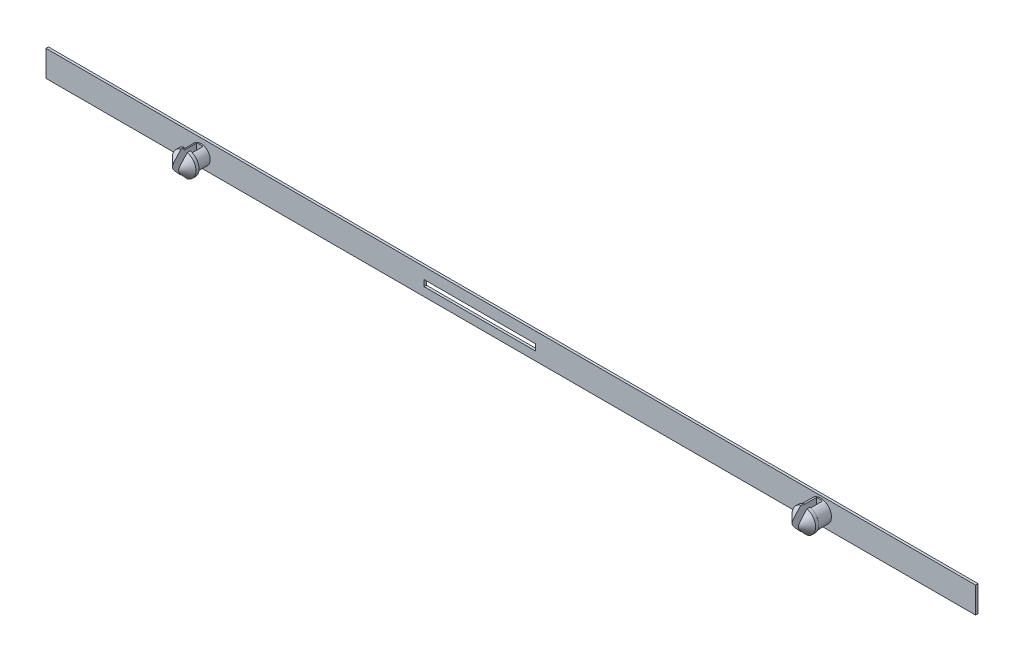
SolidWorks part; units mm, degrees
ref_plane "Přední rovina" through (0, 0, 0) normal (0, 0, 1) x (1, 0, 0)
ref_plane "Horní rovina" through (0, 0, 0) normal (0, 1, 0) x (1, 0, 0)
ref_plane "Pravá rovina" through (0, 0, 0) normal (1, 0, 0) x (0, 0, -1)
sketch "Skica2" plane through (0, 0, 0) normal (0, 0, 1) x (1, 0, 0)
  line L1 (-75, 2.1) -> (75, 2.1)
  line L2 (-75, 2.1) -> (-75, -2.1)
  line L3 (-75, -2.1) -> (75, -2.1)
  line L4 (75, 2.1) -> (75, -2.1)
  line L5 (-75, 2.1) -> (75, -2.1) construction
  line L6 (-75, -2.1) -> (75, 2.1) construction
  line L7 (4, 0.3) -> (-14, 0.3)
  line L8 (4, 0.3) -> (4, -0.7)
  line L9 (4, -0.7) -> (-14, -0.7)
  line L10 (-14, 0.3) -> (-14, -0.7)
  line L11 (4, 0.3) -> (-14, -0.7) construction
  line L12 (4, -0.7) -> (-14, 0.3) construction
  point P0 (0, 0)
  point P5 (-5, -0.2)
  dimension "D1" = 4.2
  dimension "D2" = 150
  dimension "D3" = 1
  dimension "D4" = 18
  dimension "D5" = 61
extrude "Přidat vysunutím2" add sketch "Skica2" along normal blind 0.4
sketch "Skica3" plane through (0, 0, 0.4) normal (0, 0, 1) x (1, 0, 0)
  line L0 (-75, 2.1) -> (-75, -2.1) construction
  line L1 (75, -2.1) -> (75, 2.1) construction
  line L2 (75, 2.1) -> (-75, 2.1) construction
  line L3 (-75, -2.1) -> (75, -2.1) construction
  circle A0 centre (-50, -0.2) radius 1.5
  circle A1 centre (50, 0) radius 1.75
  dimension "D1" = 3
  dimension "D3" = 3.5
  dimension "D2" = 25
  dimension "D4" = 25
  dimension "D5" = 2.3
  dimension "D6" = 1.9
extrude "Přidat vysunutím3" add sketch "Skica3" along normal blind 2.2
sketch "Skica5" plane through (0, 0, 2.6) normal (0, 0, 1) x (1, 0, 0)
  circle A0 centre (-50, -0.2) radius 1.9
  circle A1 centre (50, 0) radius 1.9
  dimension "D1" = 3.8
  dimension "D2" = 3.8
extrude "Přidat vysunutím5" add sketch "Skica5" along normal blind 2
chamfer "Zkosení2" distance 1.5 angle 45 2 edges at (51.9, 0, 4.6) (-48.1, -0.2, 4.6)
sketch "Skica7" plane through (0, 0, 4.6) normal (0, 0, 1) x (1, 0, 0)
  line L1 (-49.5, 2.3) -> (-50.5, 2.3)
  line L2 (-49.5, 2.3) -> (-49.5, -2.7)
  line L3 (-49.5, -2.7) -> (-50.5, -2.7)
  line L4 (-50.5, 2.3) -> (-50.5, -2.7)
  line L5 (-49.5, 2.3) -> (-50.5, -2.7) construction
  line L6 (-49.5, -2.7) -> (-50.5, 2.3) construction
  line L7 (49.5, 2.5) -> (50.5, 2.5)
  line L8 (49.5, 2.5) -> (49.5, -2.5)
  line L9 (49.5, -2.5) -> (50.5, -2.5)
  line L10 (50.5, 2.5) -> (50.5, -2.5)
  line L11 (49.5, 2.5) -> (50.5, -2.5) construction
  line L12 (49.5, -2.5) -> (50.5, 2.5) construction
  point P0 (-50, -0.2)
  point P5 (50, 0)
  dimension "D1" = 5
  dimension "D2" = 1
  dimension "D3" = 5
  dimension "D4" = 1
extrude "Odebrat vysunutím1" cut sketch "Skica7" against normal blind 4
equation "\"1.5.000mm\"=10"
